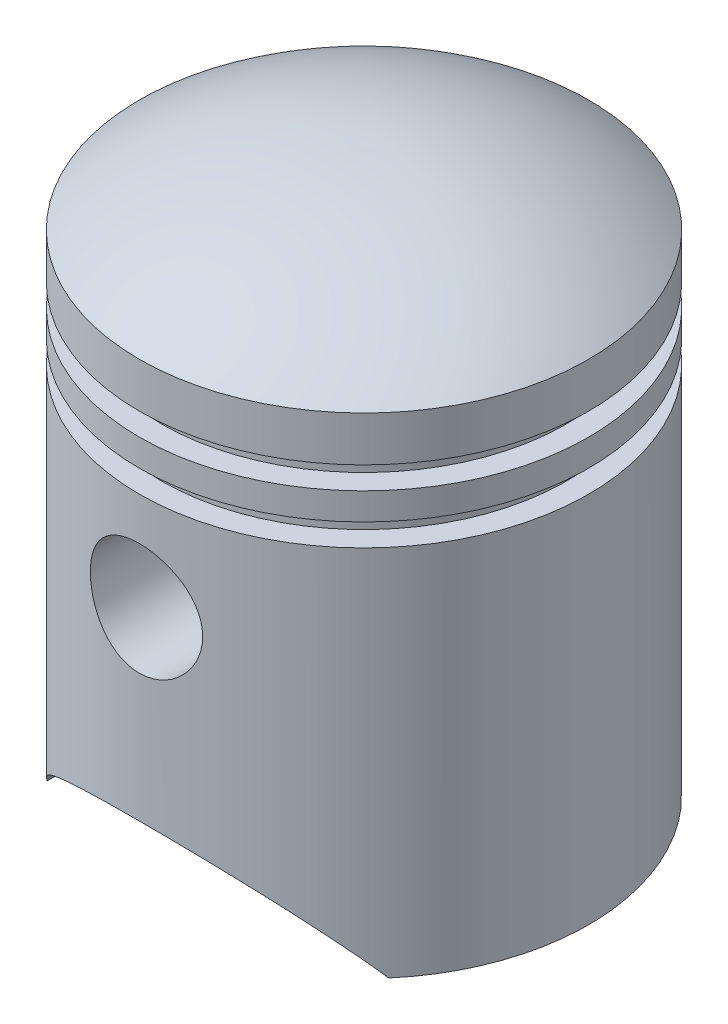
SolidWorks part; units mm, degrees
ref_plane "Front Plane" through (0, 0, 0) normal (0, 0, 1) x (1, 0, 0)
ref_plane "Top Plane" through (0, 0, 0) normal (0, 1, 0) x (1, 0, 0)
ref_plane "Right Plane" through (0, 0, 0) normal (1, 0, 0) x (0, 0, -1)
sketch "Sketch1" plane through (0, 0, 0) normal (0, 0, 1) x (1, 0, 0)
  line L0 (25, 0) -> (25, 41.5)
  line L1 (25, 49.5) -> (22.5, 49.5)
  line L2 (22.5, 49.5) -> (22.5, 47)
  line L3 (22.5, 47) -> (25, 47)
  line L4 (25, 44) -> (22.5, 44)
  line L5 (22.5, 44) -> (22.5, 41.5)
  line L6 (22.5, 41.5) -> (25, 41.5)
  line L7 (25, 49.5) -> (25, 54.5)
  line L8 (25, 44) -> (25, 47)
  line L9 (23, 0) -> (23, 39.5)
  line L10 (20.5, 39.5) -> (23, 39.5)
  line L11 (20.5, 45.5) -> (20.5, 39.5)
  line L12 (20.5, 45.5) -> (20.5, 45.5)
  line L13 (20.5, 45.5) -> (20.5, 45.5)
  line L14 (20.5, 45.5) -> (20.5, 45.5)
  line L15 (20.5, 51.5) -> (20.5, 45.5)
  line L16 (23, 51.5) -> (20.5, 51.5)
  line L17 (23, 51.5) -> (23, 53.4845)
  line L18 (25, 0) -> (23, 0)
  line L19 (0, 62.5) -> (0, 60.4994)
  arc A0 (25, 54.5) -> (0, 62.5) centre (0.9839, 22.5121) ccw
  arc A1 (23, 53.4845) -> (0, 60.4994) centre (0.9839, 22.5121) ccw
  arc A2 (23, 53.4845) -> (0.0492, 60.5006) centre (0.9839, 22.5121) ccw construction
  dimension "D4" = 40
  dimension "D1" = 25
  dimension "D2" = 54.5
  dimension "D3" = 62.5
  dimension "D5" = 5
  dimension "D6" = 2.5
  dimension "D7" = 2.5
  dimension "D8" = 3
  dimension "D9" = 2.5
  dimension "D10" = 2
revolve "Revolve1" add sketch "Sketch1" angle 360 about L19
sketch "Sketch2" plane through (0, 0, 0) normal (0, 0, 1) x (1, 0, 0)
  line L0 (-25, 0) -> (25, 0) construction
  line L1 (-19, 0) -> (19, 0)
  circle A0 centre (0, 30.5) radius 6.25
  arc A1 (-19, 0) -> (19, 0) centre (0, -13.05) cw
  point P10 (0, 10)
  dimension "D1" = 12.5
  dimension "D4" = 10
  dimension "D2" = 32
  dimension "D3" = 38
extrude "Cut-Extrude1" cut sketch "Sketch2" against normal through all both and the other way through all
sketch "Sketch3" plane through (0, 0, 0) normal (0, 0, 1) x (1, 0, 0)
  circle A0 centre (0, 30.5) radius 7.25
  circle A1 centre (0, 30.5) radius 6.25
  dimension "D1" = 14.5
  dimension "D2" = 12.5
extrude "Boss-Extrude2" add sketch "Sketch3" along normal up to surface (11.9257 mm away) from offset 12
mirror "Mirror1" about plane through (0, 0, 0) normal (0, 0, 1) of "Boss-Extrude2"
